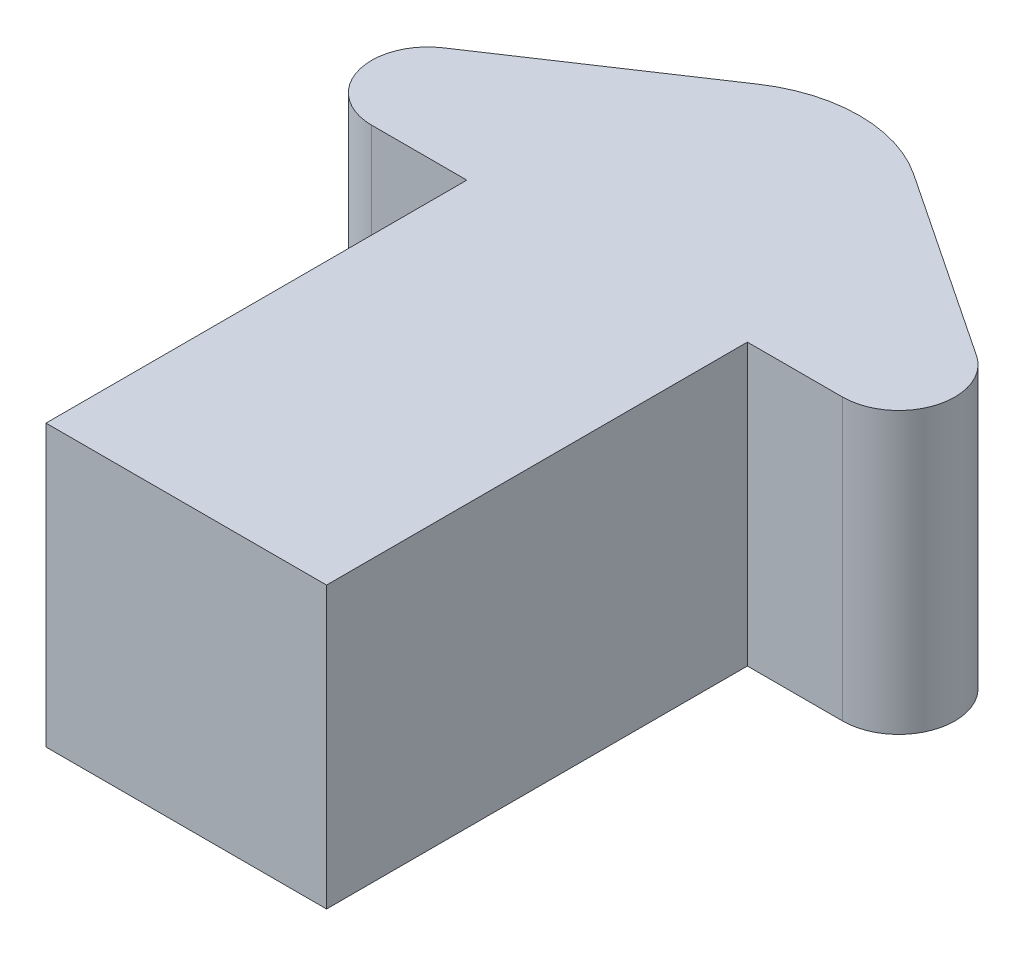
SolidWorks part; units mm, degrees
ref_plane "Front Plane" through (0, 0, 0) normal (0, 0, 1) x (1, 0, 0)
ref_plane "Top Plane" through (0, 0, 0) normal (0, 1, 0) x (1, 0, 0)
ref_plane "Right Plane" through (0, 0, 0) normal (1, 0, 0) x (0, 0, -1)
sketch "Sketch1" plane through (0, 0, 0) normal (0, 1, 0) x (1, 0, 0)
  line L0 (-10.0862, 14.9569) -> (-0.0862, 14.9569)
  line L1 (-0.0862, 14.9569) -> (9.9138, 14.9569)
  line L2 (-0.0862, 14.9569) -> (-0.0862, -0.0431)
  line L3 (-0.0862, -0.0431) -> (9.9138, -0.0431)
  line L4 (9.9138, 14.9569) -> (9.9138, -0.0431)
  line L5 (4.9138, 24.9569) -> (4.9138, 14.9569)
  line L6 (19.9138, 14.9569) -> (9.9138, 14.9569)
  line L7 (-10.0862, 14.9569) -> (4.9138, 24.9569)
  line L8 (19.9138, 14.9569) -> (4.9138, 24.9569)
  dimension "D1" = 10
  dimension "D2" = 10
  dimension "D3" = 10
  dimension "D4" = 15
  dimension "D5" = 10
extrude "Boss-Extrude1" add sketch "Sketch1" along normal blind 10 contours L4 L1 L2 L3 | L6 L8 L5 L1 | L7 L0 L1 L5
fillet "Fillet1" radius 2 2 edges at (-10.0862, 5, -14.9569) (19.9138, 5, -14.9569)
fillet "Fillet2" radius 5 1 edges at (4.9138, 5, -24.9569)
